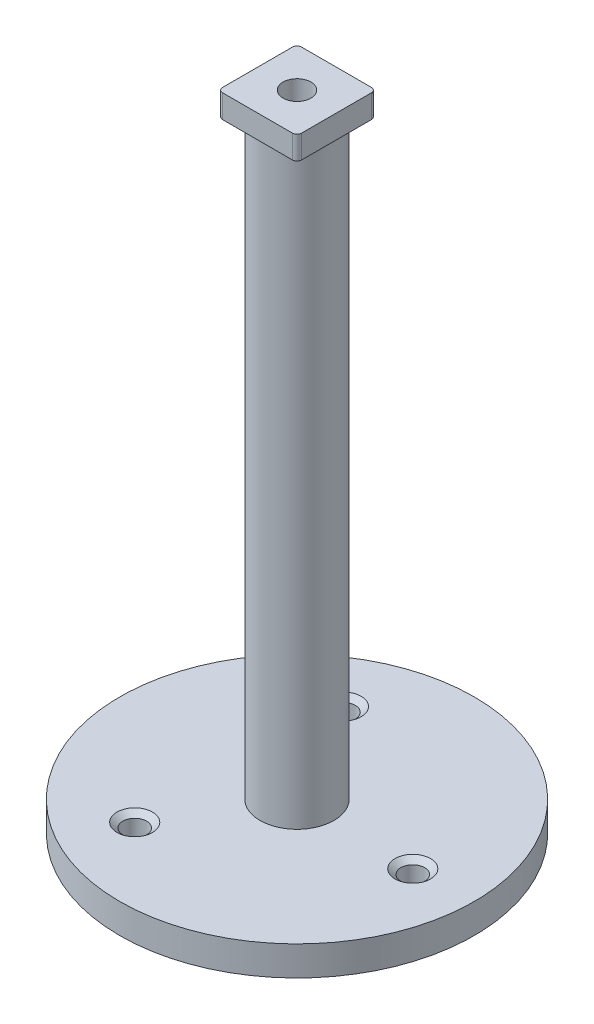
SolidWorks part; units mm, degrees
ref_plane "Front Plane" through (0, 0, 0) normal (0, 0, 1) x (1, 0, 0)
ref_plane "Top Plane" through (0, 0, 0) normal (0, 1, 0) x (1, 0, 0)
ref_plane "Right Plane" through (0, 0, 0) normal (1, 0, 0) x (0, 0, -1)
sketch "Sketch1" plane through (0, 0, 0) normal (0, 0, 1) x (1, 0, 0)
  line L0 (0, 131.177) -> (0, -23.3839) construction
  line L1 (0, 0) -> (38.1, 0)
  line L2 (38.1, 0) -> (38.1, 6.35)
  line L3 (38.1, 6.35) -> (7.9375, 6.35)
  line L4 (7.9375, 6.35) -> (7.9375, 133.35)
  line L8 (0, 133.35) -> (0, 0)
  line L9 (0, 133.35) -> (7.9375, 133.35)
  dimension "D1" = 76.2
  dimension "D2" = 6.35
  dimension "D3" = 15.875
  dimension "D4" = 127
revolve "Revolve1" add sketch "Sketch1" angle 360 about L0
sketch "Sketch2" plane through (0, 0, 0) normal (0, 1, 0) x (1, 0, 0)
  circle A0 centre (0, 0) radius 7.1438
  dimension "D1" = 14.2875
extrude "Cut-Extrude1" cut sketch "Sketch2" along normal offset from surface (120.65 mm away) 12.7 up to face at (0, 133.35, 7.9375)
sketch "Sketch5" plane through (0, 133.35, 0) normal (0, 1, 0) x (1, 0, 0)
  line L1 (-8.5, 8.5) -> (8.5, 8.5)
  line L2 (-8.5, 8.5) -> (-8.5, -8.5)
  line L3 (-8.5, -8.5) -> (8.5, -8.5)
  line L4 (8.5, 8.5) -> (8.5, -8.5)
  line L5 (-8.5, 8.5) -> (8.5, -8.5) construction
  line L6 (-8.5, -8.5) -> (8.5, 8.5) construction
  point P0 (0, 0)
  dimension "D1" = 17
  dimension "D2" = 17
extrude "Boss-Extrude3" add sketch "Sketch5" along normal blind 5
sketch "Sketch4" plane through (0, 138.35, 0) normal (0, 1, 0) x (1, 0, 0)
  circle A0 centre (0, 0) radius 3
  dimension "D1" = 6
extrude "Cut-Extrude2" cut sketch "Sketch4" against normal through all
fillet "Fillet1" radius 1 4 edges at (8.5, 135.85, 8.5) (-8.5, 135.85, 8.5) (8.5, 135.85, -8.5) (-8.5, 135.85, -8.5)
fillet "Fillet2" radius 0.25 1 edges at (0, 133.35, 7.9375)
hole_wizard "1/4-20 Tapped Hole1" positions "Sketch8" profile "Sketch9" tap size "1/4-20" standard "ANSI Inch" end condition through all
sketch "Sketch8" plane through (0, 6.35, 0) normal (0, 1, 0) x (1, 0, 0)
  circle A0 centre (0, 0) radius 25.4 construction
  point P7 (-12.2552, 22.2479)
  point P17 (25.3949, -0.5107)
  point P18 (-13.1397, -21.7373)
  point P20 (-12.2552, 22.2479)
  dimension "D1" = 50.8
  dimension "D2" = 3
sketch "Sketch9" plane through (-13.1397, 6.35, 21.7373) normal (1, 0, 0) x (0, 0, 1)
  line L0 (0, 0) -> (0, 6.35)
  line L1 (0, 6.35) -> (2.5527, 6.35)
  line L2 (2.5527, 6.35) -> (2.5527, 1.055)
  line L3 (2.5527, 1.055) -> (3.81, 0)
  line L5 (3.81, 0) -> (0, 0)
  line L6 (-2.5527, 1.055) -> (-3.81, 0) construction
  line L11 (0, -6.35) -> (0, 107.95) construction
  dimension "Thru Tap Drill Dia." = 5.1054
  dimension "Thru Tap Drill Depth" = 6.35
  dimension "Near C'Sink Dia." = 7.62
  dimension "Near C'Sink Angle" = 100
cosmetic thread "Hole Thread1" parameters "D2"=6.35
cosmetic thread "Hole Thread2" parameters "D2"=6.35
cosmetic thread "Hole Thread3" parameters "D2"=6.35
